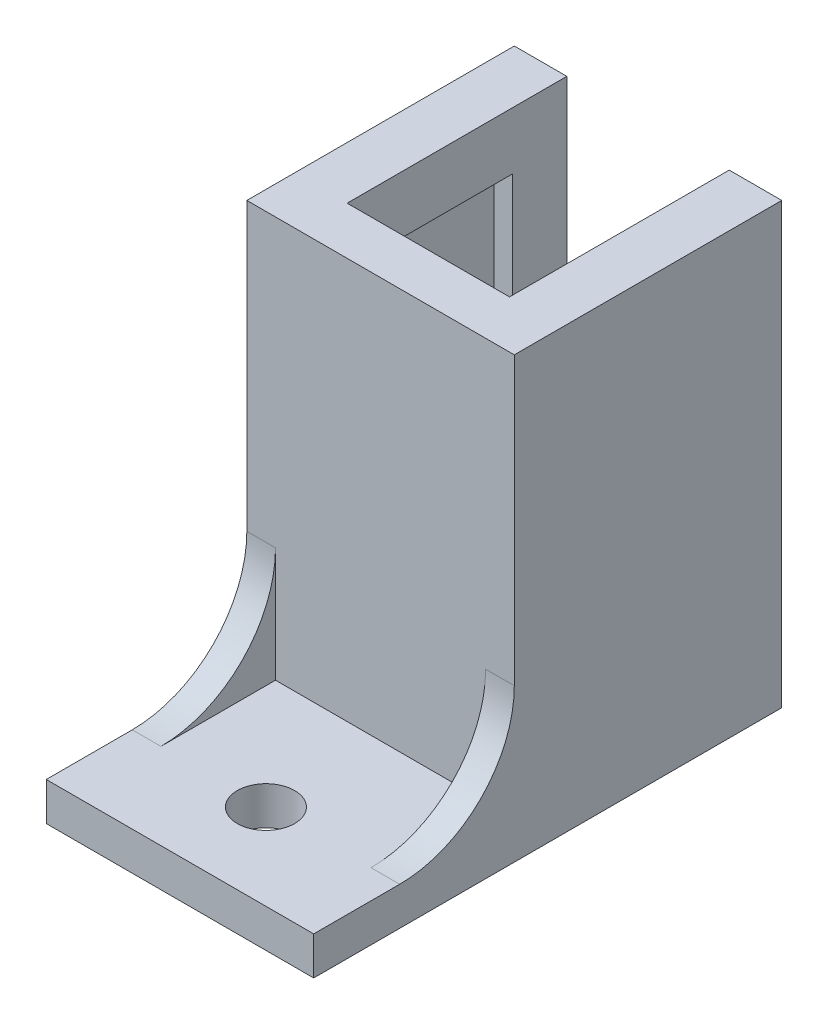
SolidWorks part; units mm, degrees
ref_plane "Front Plane" through (0, 0, 0) normal (0, 0, 1) x (1, 0, 0)
ref_plane "Top Plane" through (0, 0, 0) normal (0, 1, 0) x (1, 0, 0)
ref_plane "Right Plane" through (0, 0, 0) normal (1, 0, 0) x (0, 0, -1)
sketch "Sketch1" plane through (0, 0, 0) normal (0, 0, 1) x (1, 0, 0)
  line L1 (7, 11.5) -> (-7, 11.5)
  line L2 (7, 11.5) -> (7, -11.5)
  line L3 (7, -11.5) -> (-7, -11.5)
  line L4 (-7, 11.5) -> (-7, -11.5)
  line L5 (7, 11.5) -> (-7, -11.5) construction
  line L6 (7, -11.5) -> (-7, 11.5) construction
  point P0 (0, 0)
  dimension "D1" = 14
  dimension "D2" = 23
extrude "Boss-Extrude1" add sketch "Sketch1" along normal blind 14
sketch "Sketch2" plane through (0, -11.5, 0) normal (0, -1, 0) x (1, 0, 0)
  line L1 (5.2, 2.85) -> (-5.2, 2.85)
  line L2 (5.2, 2.85) -> (5.2, 11.5)
  line L3 (5.2, 11.5) -> (-5.2, 11.5)
  line L4 (-5.2, 2.85) -> (-5.2, 11.5)
  line L8 (4.25, 2.85) -> (-4.25, 2.85)
  line L9 (4.25, 2.85) -> (4.25, 0)
  line L10 (4.25, 0) -> (-4.25, 0)
  line L11 (-4.25, 2.85) -> (-4.25, 0)
  point P4 (0, 2.85)
  point P16 (0, 0)
  dimension "D1" = 11.5
  dimension "D2" = 8.65
  dimension "D3" = 10.4
  dimension "D4" = 8.5
extrude "Cut-Extrude1" cut sketch "Sketch2" against normal blind 20
sketch "Sketch3" plane through (0, -11.5, 0) normal (0, -1, 0) x (1, 0, 0)
  line L0 (0, 20) -> (0, 14) construction
  line L1 (7, 14) -> (-7, 14)
  line L2 (7, 14) -> (7, 24.5)
  line L3 (7, 24.5) -> (-7, 24.5)
  line L4 (-7, 14) -> (-7, 24.5)
  circle A1 centre (0, 20) radius 1.5
  dimension "D1" = 3
  dimension "D2" = 6
  dimension "D3" = 4.5
extrude "Boss-Extrude2" add sketch "Sketch3" against normal blind 2
sketch "Sketch4" plane through (-7, 0, 0) normal (-1, 0, 0) x (0, 0, 1)
  line L1 (24.5, -9.5) -> (14, -9.5) construction
  line L2 (14, 11.5) -> (14, -9.5) construction
  line L3 (14, -3.5) -> (14, -9.5)
  line L4 (14, -9.5) -> (20, -9.5)
  arc A0 (20, -9.5) -> (14, -3.5) centre (20, -3.5) cw
  dimension "D1" = 6
extrude "Boss-Extrude3" add sketch "Sketch4" against normal blind 1.5
mirror "Mirror1" about plane through (0, 0, 0) normal (1, 0, 0) of "Boss-Extrude3"
sketch "Sketch5" plane through (0, 8.5, 0) normal (0, -1, 0) x (1, 0, 0)
  line L0 (5.2, 11.5) -> (-5.2, 11.5) construction
  line L1 (4.25, 0) -> (-4.25, 0)
  line L2 (4.25, 0) -> (4.25, 11.5)
  line L3 (4.25, 11.5) -> (-4.25, 11.5)
  line L4 (-4.25, 0) -> (-4.25, 11.5)
  line L5 (7, 0) -> (4.25, 0) construction
  line L6 (-4.25, 0) -> (4.25, 0) construction
extrude "Cut-Extrude2" cut sketch "Sketch5" against normal through all
sketch "Sketch6" plane through (0, 0, 0) normal (0, 0, -1) x (-1, 0, 0)
  line L0 (-7, 11.5) -> (-7, -11.5) construction
  line L1 (-7, 0) -> (7, 0)
  line L2 (-7, 0) -> (-7, -11.5)
  line L3 (-7, -11.5) -> (7, -11.5)
  line L4 (7, 0) -> (7, -11.5)
extrude "Cut-Extrude3" [suppressed] cut sketch "Sketch6" against normal through all
